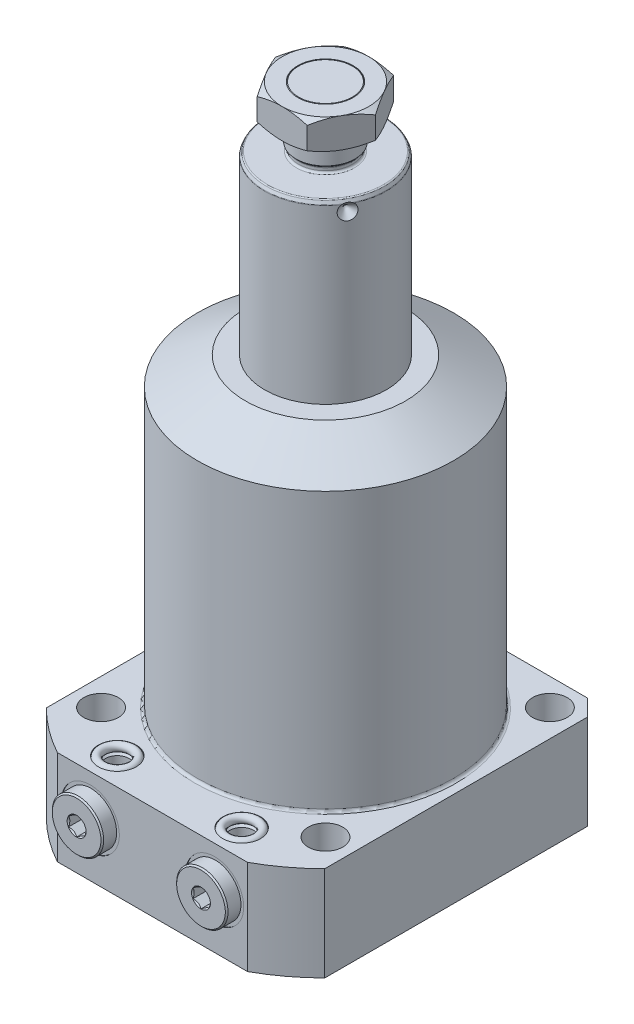
SolidWorks part; units mm, degrees
material "AISI 1020"
ref_plane "Front Plane" through (0, 0, 0) normal (0, 0, 1) x (1, 0, 0)
ref_plane "Top Plane" through (0, 0, 0) normal (0, 1, 0) x (1, 0, 0)
ref_plane "Right Plane" through (0, 0, 0) normal (1, 0, 0) x (0, 0, -1)
sketch "Sketch1" plane through (0, 0, 0) normal (0, 0, 1) x (1, 0, 0)
  line L0 (22.5, 0) -> (22.5, 176.75)
  line L1 (22.5, 176.75) -> (21.8005, 178.25)
  line L2 (21.8005, 178.25) -> (10, 178.25)
  line L3 (10, 178.25) -> (10, 180.25)
  line L4 (10, 180.25) -> (10.935, 181.185)
  line L5 (10.935, 181.185) -> (10.935, 199.5)
  line L6 (10.935, 199.5) -> (9.935, 200.5)
  line L7 (9.935, 200.5) -> (0, 200.5)
  line L8 (0, -3.075) -> (0, 64.575) construction
  line L9 (22.5, 0) -> (0, 0)
  line L10 (0, 0) -> (0, 200.5)
  line L11 (-39.1353, -35) -> (52.5913, -35) construction
  dimension "D1" = 22.25
  dimension "D2" = 45
  dimension "D3" = 20
  dimension "D4" = 21.87
  dimension "D5" = 35
  dimension "D6" = 25
  dimension "D7" = 1.5
  dimension "D8" = 45
  dimension "D9" = 1
  dimension "D10" = 19.315
  dimension "D11" = 9.935
  dimension "D12" = 235.5
revolve "Revolve2" add sketch "Sketch1" angle 360 about L8
fillet "Fillet2" radius 0.75 2 edges at (0, 178.25, -10) (0, 180.25, -10)
fillet "Fillet3" radius 0.5 2 edges at (0, 176.75, -22.5) (0, 178.25, -21.8005)
sketch "Sketch2" plane through (0, 0, 0) normal (1, 0, 0) x (0, 0, -1)
  line L0 (19.5, 174.25) -> (22.5, 171.25)
  line L1 (4.2016, 174.25) -> (7.575, 174.25) construction
  line L2 (21.482, 178.25) -> (-21.482, 178.25) construction
  line L3 (22.5, 171.25) -> (22.5, 174.25)
  line L4 (22.5, 174.25) -> (19.5, 174.25)
  line L5 (22.5, 0) -> (22.5, 176.6392) construction
  dimension "D1" = 4
  dimension "D2" = 45
  dimension "D3" = 6
revolve "Cut-Revolve1" cut sketch "Sketch2" angle 360 about L1
sketch "Sketch3" plane through (0, 200.5, 0) normal (0, 1, 0) x (1, 0, 0)
  line L1 (18.4752, 0) -> (9.2376, 16)
  line L2 (9.2376, 16) -> (-9.2376, 16)
  line L3 (-9.2376, 16) -> (-18.4752, 0)
  line L4 (-18.4752, 0) -> (-9.2376, -16)
  line L5 (-9.2376, -16) -> (9.2376, -16)
  line L6 (9.2376, -16) -> (18.4752, 0)
  circle A0 centre (0, 0) radius 16 construction
  circle A1 centre (0, 0) radius 10.25
  dimension "D2" = 20.5
  dimension "D1" = 32
extrude "Extrude3" add sketch "Sketch3" against normal blind 11
pattern_circular "CirPattern1" count 3 over 360 about axis through (0, -3.075, 0) along (0, -1, 0) of "Cut-Revolve1"
sketch "Sketch4" plane through (0, 0, 0) normal (1, 0, 0) x (0, 0, -1)
  line L0 (16, 200.5) -> (19, 200.5)
  line L1 (19, 200.5) -> (19, 198.7679)
  line L2 (19, 198.7679) -> (16, 200.5)
  line L3 (16, 195) -> (-10.9636, 195) construction
  line L4 (16, 189.5) -> (16, 200.5) construction
  line L5 (19, 191.2321) -> (16, 189.5)
  line L6 (19, 189.5) -> (19, 191.2321)
  line L7 (16, 189.5) -> (19, 189.5)
  dimension "D1" = 30
  dimension "D2" = 3
revolve "Cut-Revolve3" cut sketch "Sketch4" angle 360 about axis through (0, -3.075, 0) along (0, -1, 0)
sketch "Sketch6" plane through (0, 0, 0) normal (0, 0, 1) x (1, 0, 0)
  line L0 (0, 0) -> (0, 71.3762) construction
  line L1 (0, 113) -> (29.625, 113)
  line L2 (29.625, 113) -> (47.385, 102.7463)
  line L3 (47.385, 102.7463) -> (47.385, 0)
  line L4 (47.385, 0) -> (73.025, 0)
  line L5 (73.025, 0) -> (73.025, -35)
  line L6 (73.025, -35) -> (0, -35)
  line L7 (0, -35) -> (0, 113)
  dimension "D1" = 146.05
  dimension "D2" = 148
  dimension "D3" = 35
  dimension "D4" = 94.77
  dimension "D5" = 30
  dimension "D6" = 59.25
revolve "Revolve3" add sketch "Sketch6" angle 360 about L0
sketch "Sketch7" plane through (0, 0, 0) normal (0, 1, 0) x (-1, 0, 0)
  line L0 (0, 0) -> (0, -52.3237) construction
  line L1 (-51.5, 64) -> (51.5, 64)
  line L2 (-51.5, 64) -> (-51.5, -51.5)
  line L3 (-51.5, -51.5) -> (51.5, -51.5)
  line L4 (51.5, 64) -> (51.5, -51.5)
  dimension "D1" = 103
  dimension "D2" = 115.5
  dimension "D3" = 51.5
extrude "Cut-Extrude5" cut sketch "Sketch7" against normal through all flip side to cut
sketch "Sketch8" plane through (0, 0, 0) normal (0, 1, 0) x (-1, 0, 0)
  circle A0 centre (-41.5, 41.5) radius 6.4
  dimension "D1" = 12.8
  dimension "D2" = 41.5
  dimension "D3" = 41.5
extrude "Cut-Extrude6" cut sketch "Sketch8" against normal through all
pattern_circular "CirPattern2" count 4 over 360 about axis through (0, 0, 0) along (0, 1, 0) of "Cut-Extrude6"
chamfer "Chamfer1" distance 6 angle 45 2 edges at (-51.5, -17.5, -51.5) (51.5, -17.5, -51.5)
fillet "Fillet5" radius 1 1 edges at (0, 0, -47.385)
ref_plane "Plane1" through (0, -15, 0) normal (0, 1, 0) x (-1, 0, 0)
sketch "Sketch11" plane through (0, -15, 0) normal (0, 1, 0) x (-1, 0, 0)
  line L0 (-23, 42.9716) -> (-23, 19.7499) construction
  line L1 (-33.75, 64) -> (-33.75, 63.75)
  line L2 (35.166, 64) -> (-35.166, 64) construction
  line L3 (-33.75, 63.75) -> (-29.65, 63.75)
  line L4 (-29.65, 63.75) -> (-28.945, 63.045)
  line L5 (-28.945, 63.045) -> (-28.945, 45.03)
  line L6 (-28.945, 45.03) -> (-23, 45.03)
  line L7 (-23, 45.03) -> (-23, 64)
  line L8 (-23, 64) -> (-33.75, 64)
  dimension "D1" = 23
  dimension "D2" = 0.25
  dimension "D3" = 11.89
  dimension "D4" = 18.72
  dimension "D5" = 21.5
  dimension "D6" = 45
  dimension "D7" = 0.705
revolve "Cut-Revolve5" cut sketch "Sketch11" angle 360 about L0
ref_plane "Plane2" through (0, 0, 54) normal (0, 0, 1) x (1, 0, 0)
sketch "Sketch13" plane through (0, 0, 54) normal (0, 0, 1) x (1, 0, 0)
  line L0 (-27.375, -23) -> (-27.375, -32)
  line L1 (-27.375, -32) -> (-28.125, -32.75)
  line L2 (-28.125, -32.75) -> (-30, -32.75)
  line L3 (-30, -32.75) -> (-30, -35)
  line L5 (-30, -35) -> (-23, -35)
  line L6 (-23, -35) -> (-23, -23)
  line L7 (-23, -23) -> (-27.375, -23)
  line L8 (-23, 15.2099) -> (-23, -4.3918) construction
  line L9 (-35.166, -35) -> (35.166, -35) construction
  line L10 (-51.5, -17.5) -> (58.7286, -17.5) construction
  line L11 (-51.5, 0) -> (-51.5, -35) construction
  line L12 (-23, -12) -> (-27.375, -12)
  line L13 (-23, 0) -> (-23, -12)
  line L14 (-30, 0) -> (-23, 0)
  line L15 (-30, -2.25) -> (-30, 0)
  line L16 (-28.125, -2.25) -> (-30, -2.25)
  line L17 (-27.375, -3) -> (-28.125, -2.25)
  line L18 (-27.375, -12) -> (-27.375, -3)
  dimension "D1" = 23
  dimension "D2" = 8.75
  dimension "D3" = 12
  dimension "D4" = 2.25
  dimension "D5" = 14
  dimension "D6" = 45
  dimension "D7" = 0.75
revolve "Cut-Revolve6" cut sketch "Sketch13" angle 360 about L8
sketch "Sketch14" plane through (0, -15, 0) normal (0, 1, 0) x (-1, 0, 0)
  line L0 (-23, 32.5881) -> (-23, 43.3353) construction
  line L1 (-23, 45.03) -> (-23, 63.045) construction
  line L2 (-26.5, 69.05) -> (-32, 69.05)
  line L3 (-32, 69.05) -> (-32.5, 68.55)
  line L4 (-32.5, 68.55) -> (-32.5, 63.75)
  line L5 (-12.25, 63.75) -> (-33.75, 63.75) construction
  line L6 (-32.5, 63.75) -> (-28.6, 63.75)
  line L7 (-16.35, 63.75) -> (-29.65, 63.75) construction
  line L8 (-28.6, 63.75) -> (-28.6, 61.2474)
  line L9 (-28.6, 61.2474) -> (-23, 61.2474)
  line L10 (-23, 61.2474) -> (-23, 61.2484)
  line L11 (-23, 61.2484) -> (-26, 63.051)
  line L12 (-26, 63.051) -> (-26, 68.55)
  line L13 (-26, 68.55) -> (-26.5, 69.05)
  dimension "D1" = 11.2
  dimension "D2" = 2.5026
  dimension "D3" = 59
  dimension "D4" = 6
  dimension "D5" = 5.3
  dimension "D6" = 19
  dimension "D7" = 45
  dimension "D8" = 0.5
  dimension "D9" = 45
  dimension "D10" = 0.5
  dimension "D11" = 0.001
revolve "Revolve6" add sketch "Sketch14" angle 360 about L0
sketch "Sketch15" plane through (0, 0, 69.05) normal (0, 0, 1) x (1, 0, 0)
  line L1 (26, -16.7321) -> (26, -13.2679)
  line L2 (26, -13.2679) -> (23, -11.5359)
  line L3 (23, -11.5359) -> (20, -13.2679)
  line L4 (20, -13.2679) -> (20, -16.7321)
  line L5 (20, -16.7321) -> (23, -18.4641)
  line L6 (23, -18.4641) -> (26, -16.7321)
  circle A0 centre (23, -15) radius 3 construction
  dimension "D1" = 6
extrude "Cut-Extrude8" cut sketch "Sketch15" against normal blind 5.3
mirror "Mirror1" about plane through (0, 0, 0) normal (1, 0, 0) of "Cut-Extrude8", "Revolve6", "Cut-Revolve6", "Cut-Revolve5"
sketch "Sketch16" plane through (0, 0, 54) normal (0, 0, 1) x (1, 0, 0)
  line L0 (-51.5, -17.5) -> (60.0467, -17.5) construction
  line L1 (-23, 9.3219) -> (-23, -15.1063) construction
  line L2 (-23, -32) -> (-23, -23) construction
  line L3 (-35.166, 0) -> (35.166, 0) construction
  line L4 (-51.5, 0) -> (-51.5, -35) construction
  circle A0 centre (-28.5, -0.75) radius 1.5
  circle A1 centre (-28.5, -34.25) radius 1.5
  dimension "D1" = 3
  dimension "D3" = 0.75
  dimension "D2" = 11
revolve "Revolve7" add sketch "Sketch16" angle 360 about L1
mirror "Mirror3" about plane through (0, 0, 0) normal (1, 0, 0) of bodies 128 131
